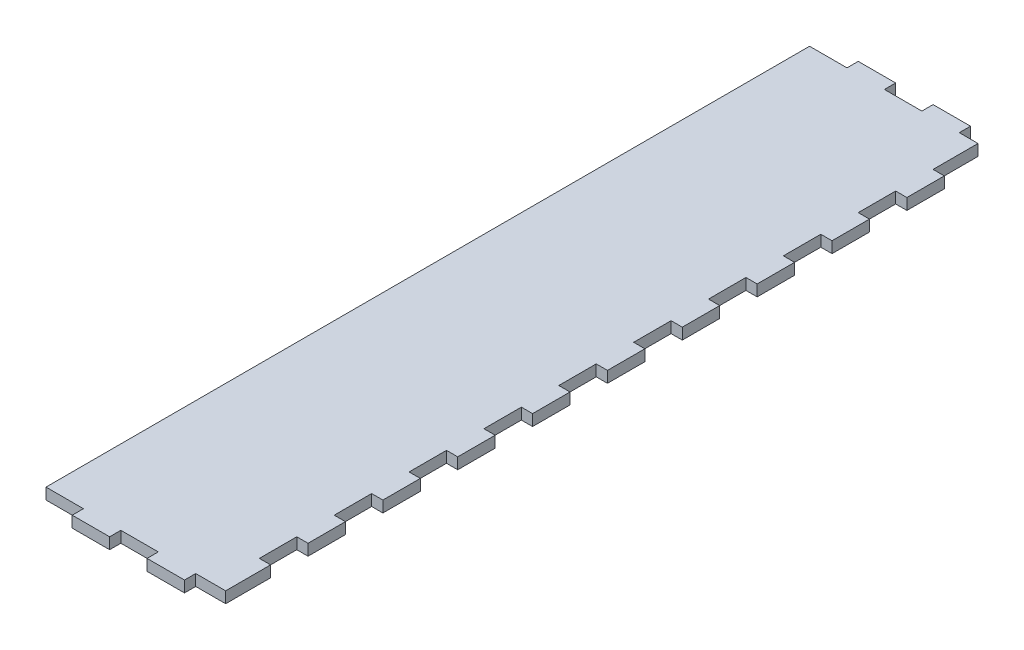
SolidWorks part; units mm, degrees
ref_plane "Front Plane" through (0, 0, 0) normal (0, 0, 1) x (1, 0, 0)
ref_plane "Top Plane" through (0, 0, 0) normal (0, 1, 0) x (1, 0, 0)
ref_plane "Right Plane" through (0, 0, 0) normal (1, 0, 0) x (0, 0, -1)
sketch "Sketch1" plane through (0, 0, 0) normal (0, 1, 0) x (1, 0, 0)
  line L1 (0, 0) -> (45, 0)
  line L2 (0, 0) -> (0, 204)
  line L3 (0, 204) -> (45, 204)
  line L4 (45, 0) -> (45, 204)
  dimension "D1" = 45
  dimension "D2" = 204
extrude "Boss-Extrude1" add sketch "Sketch1" along normal blind 3 contours L2 L3 L4 L1
sketch "Sketch2" plane through (0, 0, 0) normal (0, 0, 1) x (1, 0, 0)
  line L5 (0, 3) -> (45, 3) construction
  line L6 (40, 3) -> (30, 3)
  line L7 (40, 3) -> (40, 0)
  line L8 (40, 0) -> (30, 0)
  line L9 (30, 3) -> (30, 0)
  line L10 (0, 0) -> (45, 0) construction
  line L11 (45, 3) -> (45, 0) construction
  dimension "D1" = 10
  dimension "D2" = 5
extrude "Boss-Extrude2" add sketch "Sketch2" along normal blind 3
pattern_linear "LPattern1" count 2 spacing 20 along (-1, 0, 0) of "Boss-Extrude2"
sketch "Sketch3" plane through (0, 0, -204) normal (0, 0, -1) x (-1, 0, 0)
  line L0 (0, 3) -> (-45, 3) construction
  line L5 (-40, 3) -> (-30, 3)
  line L6 (-40, 3) -> (-40, 0)
  line L7 (-40, 0) -> (-30, 0)
  line L8 (-30, 3) -> (-30, 0)
  line L9 (-45, 3) -> (-45, 0) construction
  line L11 (0, 0) -> (-45, 0) construction
  point P10 (0, 0)
  point P11 (0, 0)
  dimension "D1" = 5
  dimension "D2" = 10
extrude "Boss-Extrude3" add sketch "Sketch3" along normal blind 3
pattern_linear "LPattern2" count 2 spacing 20 along (-1, 0, 0) of "Boss-Extrude3"
sketch "Sketch4" plane through (45, 0, 0) normal (1, 0, 0) x (0, 0, -1)
  line L11 (0, 3) -> (204, 3) construction
  line L12 (0, 0) -> (12, 0)
  line L13 (0, 0) -> (0, 3)
  line L14 (0, 3) -> (12, 3)
  line L15 (12, 0) -> (12, 3)
  line L16 (0, 0) -> (204, 0) construction
  line L17 (22, 0) -> (32, 0)
  line L18 (22, 0) -> (22, 3)
  line L19 (22, 3) -> (32, 3)
  line L20 (32, 0) -> (32, 3)
  line L21 (42, 0) -> (42, 3)
  line L22 (42, 0) -> (52, 0)
  line L23 (52, 0) -> (52, 3)
  line L24 (42, 3) -> (52, 3)
  line L25 (62, 0) -> (62, 3)
  line L26 (62, 0) -> (72, 0)
  line L27 (72, 0) -> (72, 3)
  line L28 (62, 3) -> (72, 3)
  line L29 (82, 0) -> (82, 3)
  line L30 (82, 0) -> (92, 0)
  line L31 (92, 0) -> (92, 3)
  line L32 (82, 3) -> (92, 3)
  line L33 (102, 0) -> (102, 3)
  line L34 (102, 0) -> (112, 0)
  line L35 (112, 0) -> (112, 3)
  line L36 (102, 3) -> (112, 3)
  line L37 (122, 0) -> (122, 3)
  line L38 (122, 0) -> (132, 0)
  line L39 (132, 0) -> (132, 3)
  line L40 (122, 3) -> (132, 3)
  line L41 (142, 0) -> (142, 3)
  line L42 (142, 0) -> (152, 0)
  line L43 (152, 0) -> (152, 3)
  line L44 (142, 3) -> (152, 3)
  line L45 (162, 0) -> (162, 3)
  line L46 (162, 0) -> (172, 0)
  line L47 (172, 0) -> (172, 3)
  line L48 (162, 3) -> (172, 3)
  line L49 (182, 0) -> (182, 3)
  line L50 (182, 0) -> (192, 0)
  line L51 (192, 0) -> (192, 3)
  line L52 (182, 3) -> (192, 3)
  dimension "D1" = 12
  dimension "D2" = 10
  dimension "D3" = 10
  dimension "D4" = 9
extrude "Boss-Extrude4" add sketch "Sketch4" along normal blind 3
